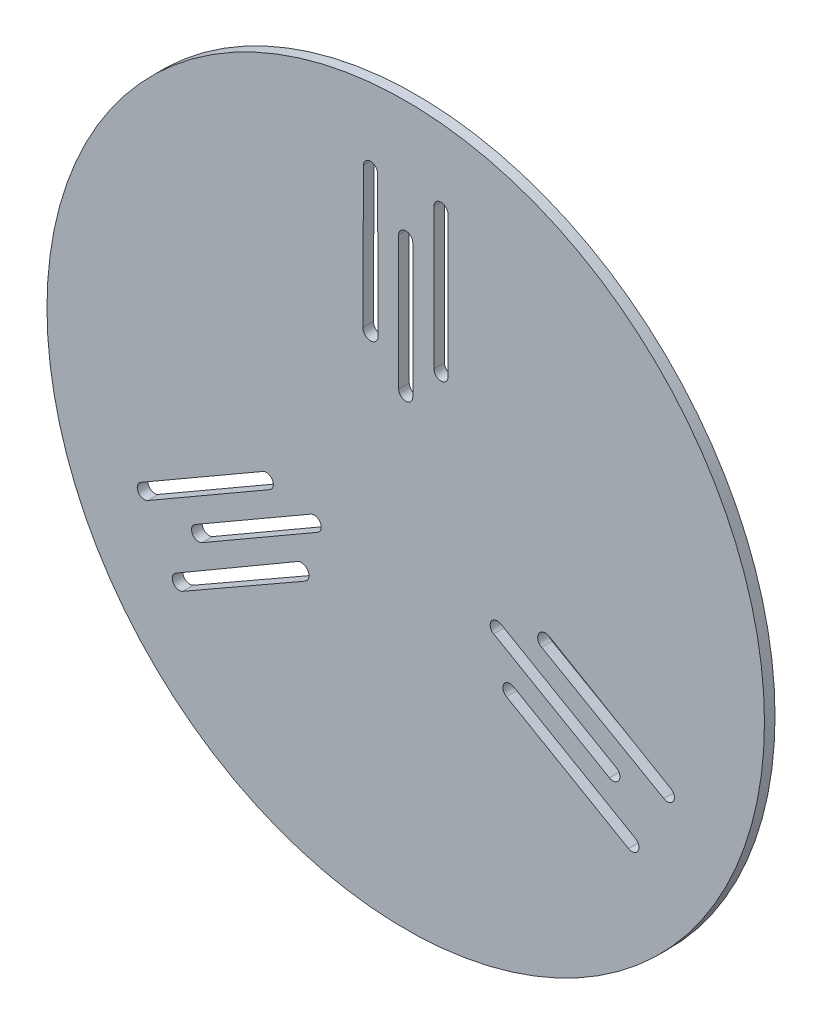
SolidWorks part; units mm, degrees
ref_plane "Front Plane" through (0, 0, 0) normal (0, 0, 1) x (1, 0, 0)
ref_plane "Top Plane" through (0, 0, 0) normal (0, 1, 0) x (1, 0, 0)
ref_plane "Right Plane" through (0, 0, 0) normal (1, 0, 0) x (0, 0, -1)
sketch "Sketch1" plane through (0, 0, 0) normal (0, 0, 1) x (1, 0, 0)
  line L0 (0, 0) -> (0, 28) construction
  line L1 (0, 0) -> (88.2126, -50.9296) construction
  line L2 (0, 0) -> (-88.2126, -50.9296) construction
  line L3 (-2, 67.9104) -> (-2, 30)
  line L4 (2, 67.9104) -> (2, 30)
  line L5 (-1164.1563, 40) -> (-93.6765, 40) construction
  line L6 (11.9991, 40) -> (12, 40) construction
  line L8 (-12, 80) -> (-12.1654, 40)
  line L9 (-8, 80) -> (-7.8346, 40)
  line L10 (8, 79.9409) -> (8, 39.9409)
  line L11 (12, 79.9409) -> (12, 39.9409)
  line L13 (59.8121, -32.2232) -> (26.9808, -13.2679)
  line L14 (57.8121, -35.6873) -> (24.9808, -16.7321)
  line L15 (75.282, -29.6077) -> (40.7237, -9.4645)
  line L16 (73.282, -33.0718) -> (38.5583, -13.215)
  line L17 (65.2308, -46.8986) -> (30.5898, -26.8986)
  line L18 (63.2308, -50.3627) -> (28.5898, -30.3627)
  line L19 (28.6415, -30.3915) -> (28.641, -30.3923) construction
  line L21 (-57.8121, -35.6873) -> (-24.9808, -16.7321)
  line L22 (-59.8121, -32.2232) -> (-26.9808, -13.2679)
  line L23 (-63.282, -50.3923) -> (-28.5583, -30.5355)
  line L24 (-65.282, -46.9282) -> (-30.7237, -26.785)
  line L25 (-73.2308, -33.0422) -> (-38.5898, -13.0422)
  line L26 (-75.2308, -29.5781) -> (-40.5898, -9.5781)
  line L27 (-40.6406, -9.6085) -> (-40.641, -9.6077) construction
  line L28 (8, 40) -> (8.0009, 40) construction
  line L31 (11.9991, 40) -> (12, 40) construction
  line L32 (93.6765, 40) -> (1008.0009, 40) construction
  circle A0 centre (0, 0) radius 101.8592
  arc A1 (-2, 30) -> (2, 30) centre (0, 30) ccw
  arc A2 (2, 67.9104) -> (-2, 67.9104) centre (0, 67.9104) ccw
  arc A3 (-12.1653, 40.0179) -> (-7.8347, 40.0179) centre (-10, 40) ccw
  arc A4 (8.0009, 40) -> (11.9991, 40) centre (10, 39.9409) ccw
  arc A5 (-8, 80) -> (-12, 80) centre (-10, 80) ccw
  arc A6 (12, 79.9409) -> (8, 79.9409) centre (10, 79.9409) ccw
  arc A7 (26.9808, -13.2679) -> (24.9808, -16.7321) centre (25.9808, -15) ccw
  arc A8 (57.8121, -35.6873) -> (59.8121, -32.2232) centre (58.8121, -33.9552) ccw
  arc A9 (40.7392, -9.4735) -> (38.5739, -13.2239) centre (39.641, -11.3397) ccw
  arc A10 (30.6406, -26.929) -> (28.6415, -30.3915) centre (29.5898, -28.6307) ccw
  arc A11 (73.282, -33.0718) -> (75.282, -29.6077) centre (74.282, -31.3397) ccw
  arc A12 (63.2308, -50.3627) -> (65.2308, -46.8986) centre (64.2308, -48.6307) ccw
  arc A13 (-24.9808, -16.7321) -> (-26.9808, -13.2679) centre (-25.9808, -15) ccw
  arc A14 (-59.8121, -32.2232) -> (-57.8121, -35.6873) centre (-58.8121, -33.9552) ccw
  arc A15 (-28.5739, -30.5444) -> (-30.7392, -26.794) centre (-29.641, -28.6603) ccw
  arc A16 (-38.6415, -13.071) -> (-40.6406, -9.6085) centre (-39.5898, -11.3102) ccw
  arc A17 (-65.282, -46.9282) -> (-63.282, -50.3923) centre (-64.282, -48.6603) ccw
  arc A18 (-75.2308, -29.5781) -> (-73.2308, -33.0422) centre (-74.2308, -31.3102) ccw
  point P14 (0, 40)
  point P15 (-10, 40)
  point P18 (0, 40)
  point P19 (10, 39.9409)
  point P48 (34.641, -20)
  point P49 (39.641, -11.3397)
  point P51 (34.641, -20)
  point P52 (29.5898, -28.6307)
  point P77 (-34.641, -20)
  point P78 (-29.641, -28.6603)
  point P80 (-34.641, -20)
  point P81 (-39.5898, -11.3102)
  point P100 (0, 0)
  dimension "D1" = 203.7183
  dimension "D5" = 4
  dimension "D6" = 4
  dimension "D13" = 4
  dimension "D14" = 4
  dimension "D2" = 120
  dimension "D3" = 120
  dimension "D4" = 30
  dimension "D8" = 10
  dimension "D9" = 10
  dimension "D10" = 10
  dimension "D11" = 40
  dimension "D12" = 40
  dimension "D15" = 3
extrude "Boss-Extrude1" add sketch "Sketch1" along normal blind 3 contours A0 A18 L26 A16 L25 A17 L24 A15 L23 A14 L22 A13 L21 A12 L18 A10 L17 A11 L16 A9 L15 A8 L14 A7 L13 A6 L11 A4 L10 A5 L9 A3 L8 A2 L4 A1
